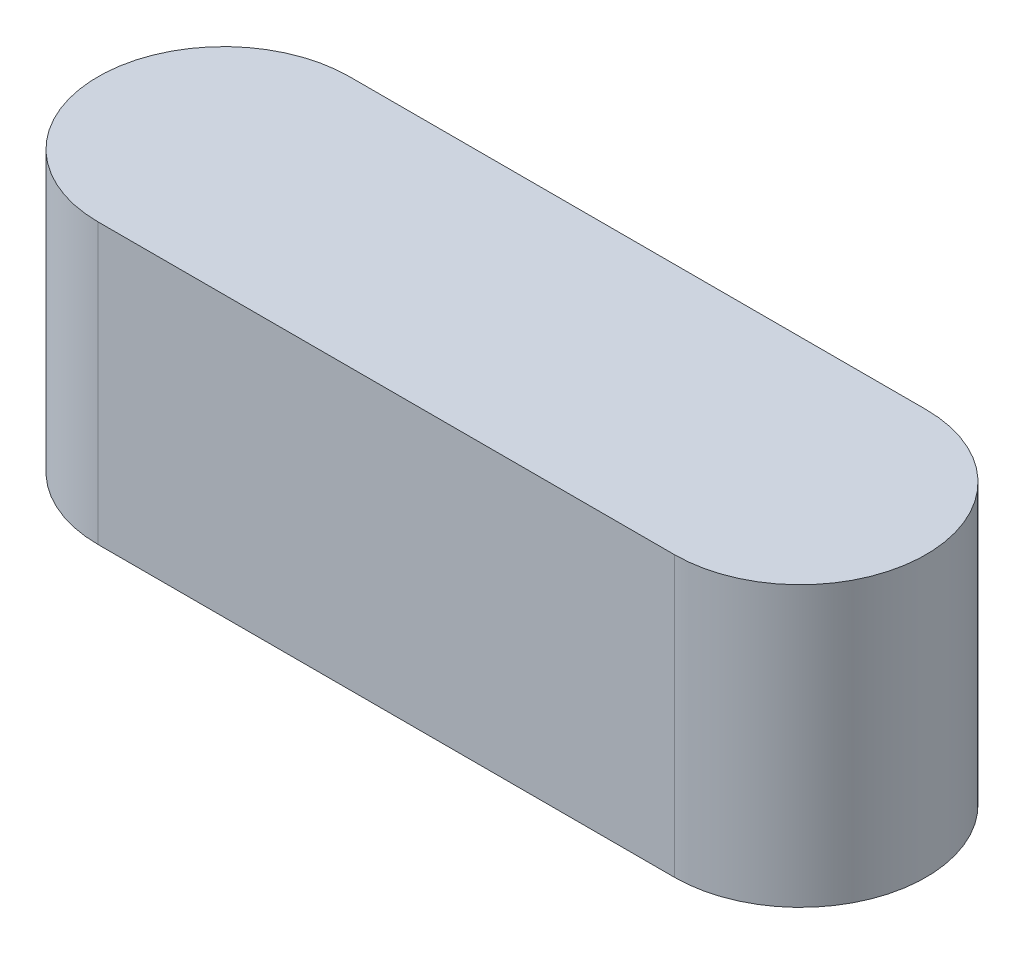
SolidWorks part; units mm, degrees
ref_plane "前视基准面" through (0, 0, 0) normal (0, 0, 1) x (1, 0, 0)
ref_plane "上视基准面" through (0, 0, 0) normal (0, 1, 0) x (1, 0, 0)
ref_plane "右视基准面" through (0, 0, 0) normal (1, 0, 0) x (0, 0, -1)
sketch "草图1" plane through (0, 0, 0) normal (0, 1, 0) x (1, 0, 0)
  line L0 (0, 0) -> (55.7, 0) construction
  line L1 (0, 12.15) -> (55.7, 12.15)
  line L2 (0, -12.15) -> (55.7, -12.15)
  arc A0 (0, 12.15) -> (0, -12.15) centre (0, 0) ccw
  arc A1 (55.7, -12.15) -> (55.7, 12.15) centre (55.7, 0) ccw
  point P3 (27.85, 0)
  dimension "D1" = 12.15
  dimension "D2" = 55.7
extrude "凸台-拉伸1" add sketch "草图1" along normal blind 27
sketch "草图2" plane through (0, 0, 0) normal (0, -1, 0) x (1, 0, 0)
  line L0 (27.85, -0.85) -> (27.85, 12.15) construction
  line L1 (20.35, -8.85) -> (35.35, -8.85)
  line L2 (20.35, -8.85) -> (20.35, -0.85)
  line L3 (20.35, -0.85) -> (35.35, -0.85)
  line L4 (35.35, -8.85) -> (35.35, -0.85)
  line L5 (0, 12.15) -> (55.7, 12.15) construction
  dimension "D1" = 15
  dimension "D2" = 8
  dimension "D3" = 13
extrude "凸台-拉伸2" add sketch "草图2" along normal blind 5
